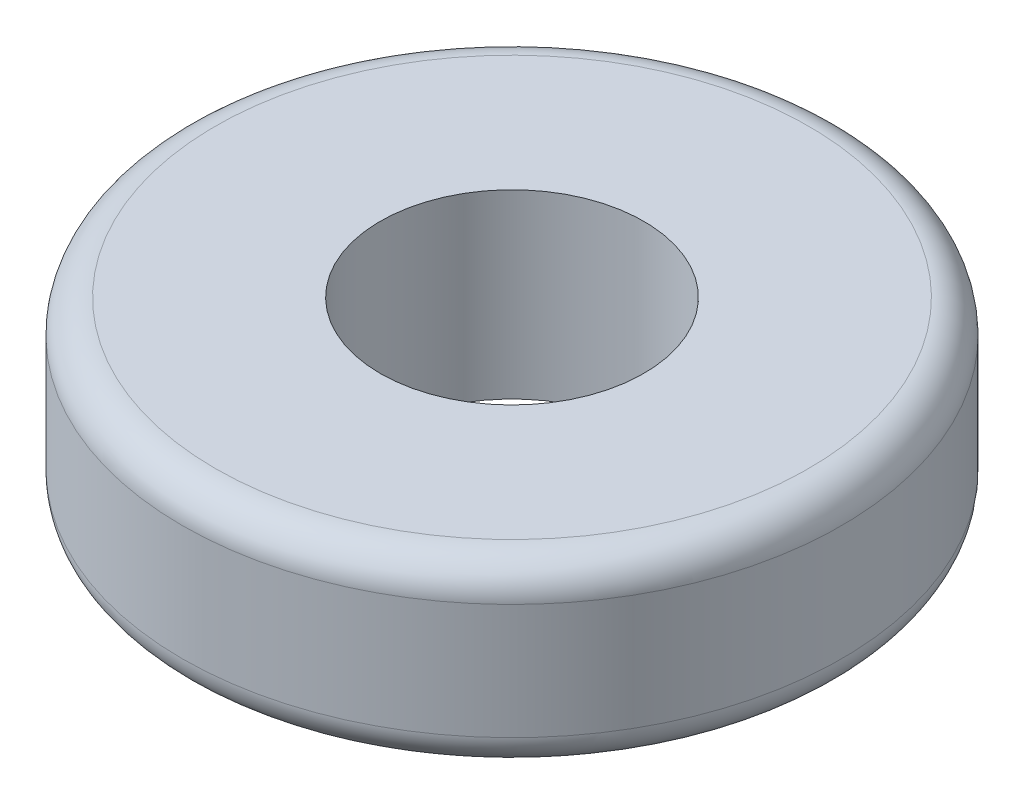
SolidWorks part; units mm, degrees
ref_plane "Front Plane" through (0, 0, 0) normal (0, 0, 1) x (1, 0, 0)
ref_plane "Top Plane" through (0, 0, 0) normal (0, 1, 0) x (1, 0, 0)
ref_plane "Right Plane" through (0, 0, 0) normal (1, 0, 0) x (0, 0, -1)
sketch "Sketch1" plane through (0, 0, 0) normal (0, 1, 0) x (1, 0, 0)
  circle A0 centre (0, 0) radius 4
  circle A1 centre (0, 0) radius 10
  dimension "D1" = 8
  dimension "D2" = 20
extrude "Boss-Extrude1" add sketch "Sketch1" along normal blind 5.5
fillet "Fillet1" radius 1 2 edges at (0, 0, 10) (0, 5.5, 10)
